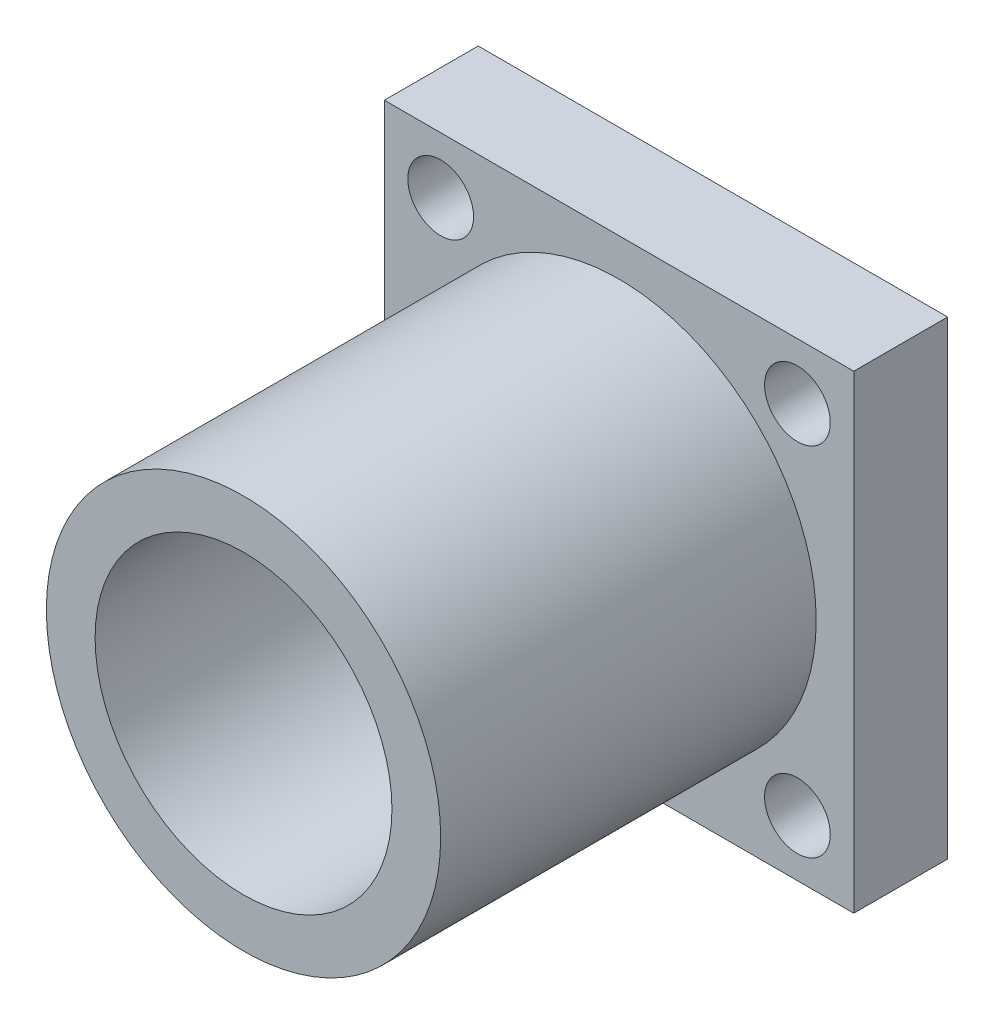
SolidWorks part; units mm, degrees
ref_plane "前视基准面" through (0, 0, 0) normal (0, 0, 1) x (1, 0, 0)
ref_plane "上视基准面" through (0, 0, 0) normal (0, 1, 0) x (1, 0, 0)
ref_plane "右视基准面" through (0, 0, 0) normal (1, 0, 0) x (0, 0, -1)
sketch "草图1" plane through (0, 0, 0) normal (0, 0, 1) x (1, 0, 0)
  line L1 (12.5, -12.5) -> (-12.5, -12.5)
  line L2 (12.5, -12.5) -> (12.5, 12.5)
  line L3 (12.5, 12.5) -> (-12.5, 12.5)
  line L4 (-12.5, -12.5) -> (-12.5, 12.5)
  line L5 (0, 12.5) -> (0, -12.5) construction
  line L6 (12.5, 0) -> (-12.5, 0) construction
  circle A0 centre (0, 0) radius 7.905 construction
  circle A1 centre (-9.5, 9.5) radius 1.75
  circle A2 centre (-9.5, -9.5) radius 1.75
  circle A3 centre (9.5, -9.5) radius 1.75
  circle A4 centre (9.5, 9.5) radius 1.75
  point P0 (0, 0)
  dimension "D3" = 15.81
  dimension "D4" = 3.5
  dimension "D1" = 25
  dimension "D2" = 25
  dimension "D5" = 3
  dimension "D6" = 3
extrude "凸台-拉伸1" add sketch "草图1" along normal blind 5
sketch "草图2" plane through (0, 0, 5) normal (0, 0, 1) x (1, 0, 0)
  circle A0 centre (0, 0) radius 7.905 construction
  circle A1 centre (0, 0) radius 7.905
extrude "切除-拉伸1" cut sketch "草图2" against normal blind 5
sketch "草图3" plane through (0, 0, 5) normal (0, 0, 1) x (1, 0, 0)
  circle A0 centre (0, 0) radius 7.905 construction
  circle A1 centre (0, 0) radius 7.905
  circle A2 centre (0, 0) radius 10.5
  dimension "D1" = 21
extrude "凸台-拉伸2" add sketch "草图3" along normal blind 20
